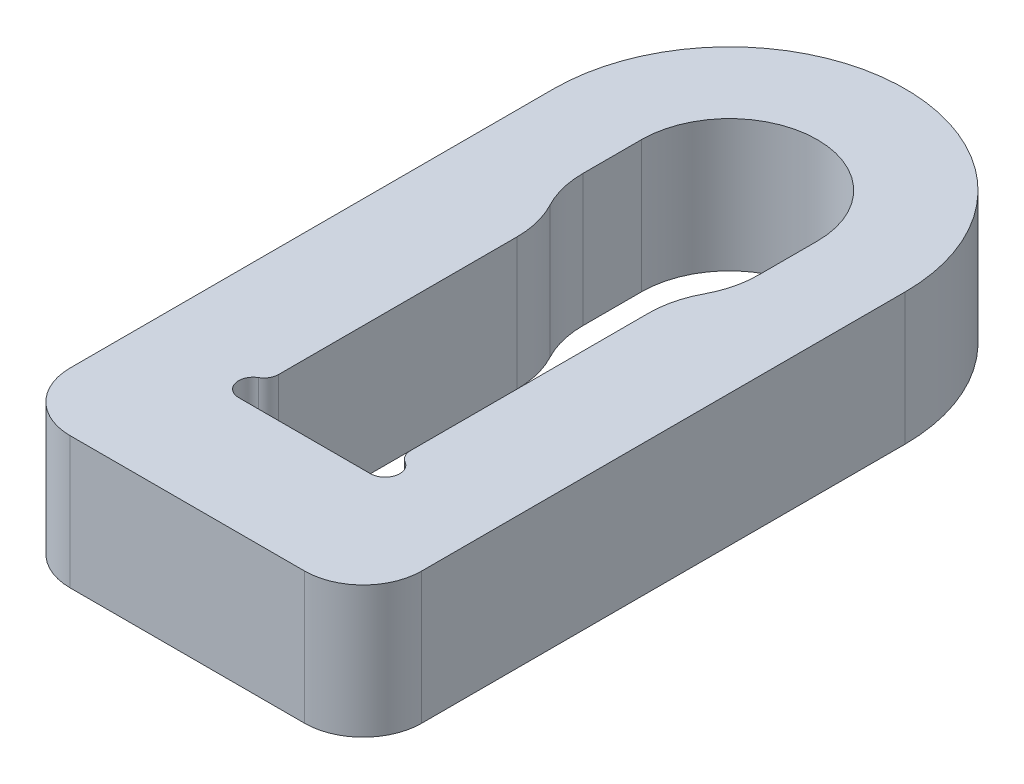
SolidWorks part; units mm, degrees
ref_plane "Front Plane" through (0, 0, 0) normal (0, 0, 1) x (1, 0, 0)
ref_plane "Top Plane" through (0, 0, 0) normal (0, 1, 0) x (1, 0, 0)
ref_plane "Right Plane" through (0, 0, 0) normal (1, 0, 0) x (0, 0, -1)
sketch "Sketch1" plane through (0, 0, 0) normal (0, 1, 0) x (1, 0, 0)
  line L1 (3, 0) -> (3, -2)
  line L2 (-3, 0) -> (-3, -2)
  line L3 (-6, 0) -> (-6, -5)
  line L4 (2.25, -5) -> (2.25, -13.134)
  line L5 (-6, -5) -> (-6, -16.5)
  line L6 (-4, -18.5) -> (4, -18.5)
  line L7 (6, -16.5) -> (6, -5)
  line L8 (-2.25, -5) -> (-2.25, -13.134)
  line L9 (6, -5) -> (6, 0)
  line L10 (0, 10.3766) -> (0, -18.5) construction
  line L11 (-10.8671, -5) -> (11.6584, -5) construction
  line L14 (-2.25, -14.5) -> (2.25, -14.5)
  line L16 (-2.25, -5) -> (2.25, -14.5) construction
  line L17 (-2.25, -14.5) -> (2.25, -5) construction
  arc A0 (3, 0) -> (-3, 0) centre (0, 0) ccw
  arc A1 (-2.25, -5) -> (-2.625, -3.5) centre (-5.4375, -5) ccw
  arc A2 (-6, 0) -> (6, 0) centre (0, 0) cw
  arc A3 (4, -18.5) -> (6, -16.5) centre (4, -16.5) ccw
  arc A4 (-4, -18.5) -> (-6, -16.5) centre (-4, -16.5) cw
  arc A5 (2.25, -5) -> (2.625, -3.5) centre (5.4375, -5) cw
  arc A6 (2.625, -3.5) -> (3, -2) centre (-0.1875, -2) ccw
  arc A7 (-2.625, -3.5) -> (-3, -2) centre (0.1875, -2) cw
  arc A8 (2.25, -14.5) -> (2.5, -13.567) centre (2.25, -14) ccw
  arc A9 (2.5, -13.567) -> (2.25, -13.134) centre (2.75, -13.134) cw
  arc A10 (-2.25, -14.5) -> (-2.5, -13.567) centre (-2.25, -14) cw
  arc A11 (-2.5, -13.567) -> (-2.25, -13.134) centre (-2.75, -13.134) ccw
  point P19 (0, -9.75)
  dimension "D1" = 3
  dimension "D3" = 6
  dimension "D4" = 2
  dimension "D8" = 0.5
  dimension "D2" = 2
  dimension "D5" = 4
  dimension "D6" = 5
  dimension "D7" = 9.5
  dimension "D9" = 4.5
extrude "Boss-Extrude1" add sketch "Sketch1" along normal blind 4.5
